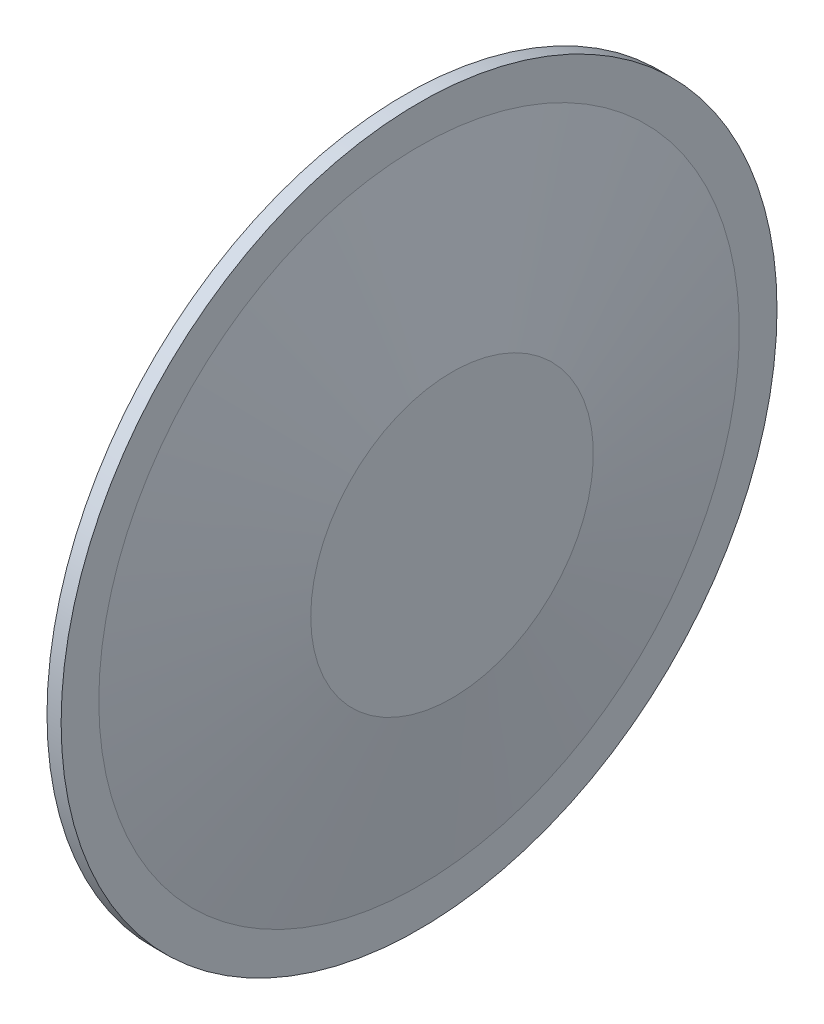
SolidWorks part; units mm, degrees
ref_plane "Front" through (0, 0, 0) normal (0, 0, 1) x (1, 0, 0)
ref_plane "Top" through (0, 0, 0) normal (0, 1, 0) x (1, 0, 0)
ref_plane "Right" through (0, 0, 0) normal (1, 0, 0) x (0, 0, -1)
sketch "Skizze1" plane through (0, 0, 0) normal (0, 0, 1) x (1, 0, 0)
  line L0 (0, 0) -> (27.7436, 0) construction
  line L1 (0, 33.863) -> (0, 38)
  line L2 (0, 38) -> (1.5, 38)
  line L3 (1.5, 38) -> (1.5, 34)
  line L4 (1.5, 34) -> (5, 15)
  line L5 (5, 15) -> (5, 0)
  line L6 (5, 0) -> (3.5, 0)
  line L7 (3.5, 0) -> (3.5, 14.863)
  line L8 (3.5, 14.863) -> (0, 33.863)
  dimension "D1" = 3.5
  dimension "D2" = 1.5
  dimension "D3" = 76
  dimension "D4" = 68
  dimension "D5" = 30
  dimension "D6" = 1.5
  dimension "D7" = 1.5
revolve "Rotation1" add sketch "Skizze1" angle 360 about L0
sketch "Skizze2" plane through (0, 0, 0) normal (1, 0, 0) x (0, 0, -1)
  line L0 (9.525, 0) -> (-9.525, 0) construction
  circle A0 centre (9.525, 0) radius 1.575
  circle A1 centre (-9.525, 0) radius 1.575
  point P6 (0, 0)
  dimension "D1" = 3.15
  dimension "D2" = 19.05
extrude "Aufsatz-Linear austragen1" add sketch "Skizze2" against normal blind 9 from surface at 3.5 starting at face at (3.5, 0, 14.863)
fillet "Verrundung1" radius 1 2 edges at (-5.5, 0, 7.95) (-5.5, 0, -11.1)
fillet "Verrundung2" radius 2.5 2 edges at (3.5, 0, -11.1) (3.5, 0, 7.95)
